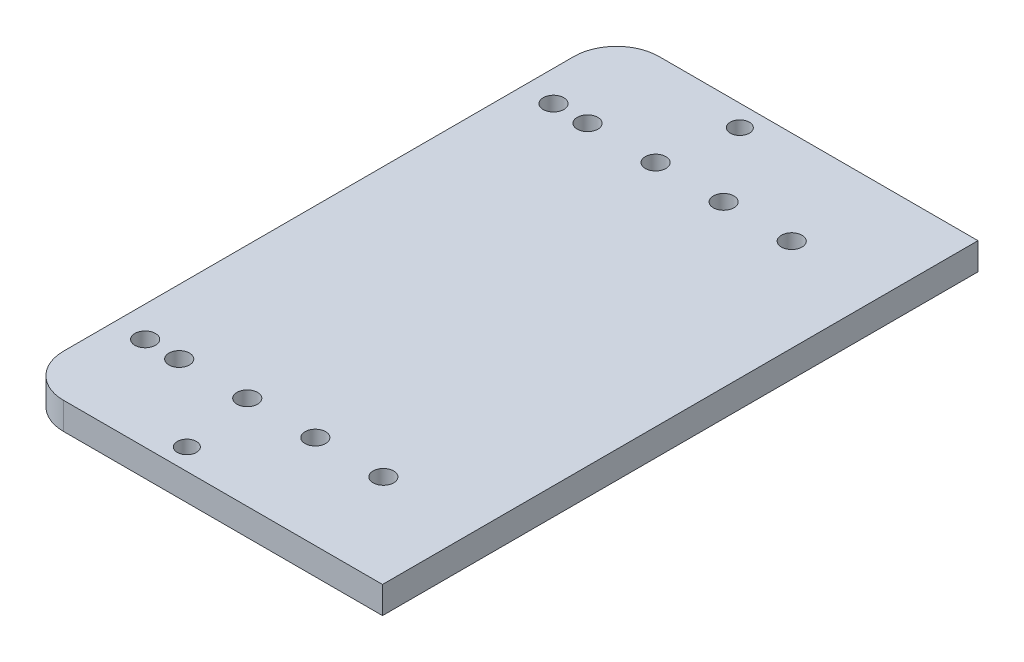
SolidWorks part; units mm, degrees
material "Acrylic (Medium-high impact)"
ref_plane "Front Plane" through (0, 0, 0) normal (0, 0, 1) x (1, 0, 0)
ref_plane "Top Plane" through (0, 0, 0) normal (0, 1, 0) x (1, 0, 0)
ref_plane "Right Plane" through (0, 0, 0) normal (1, 0, 0) x (0, 0, -1)
sketch "Sketch1" plane through (0, 0, 0) normal (0, 1, 0) x (1, 0, 0)
  line L1 (-202.6063, -35.5695) -> (-117.6063, -35.5695)
  line L2 (-202.6063, -35.5695) -> (-202.6063, -175.5695)
  line L3 (-202.6063, -175.5695) -> (-117.6063, -175.5695)
  line L4 (-117.6063, -35.5695) -> (-117.6063, -175.5695)
  dimension "D1" = 140
  dimension "D2" = 85
  dimension "D3" = 35.5695
extrude "Boss-Extrude1" add sketch "Sketch1" along normal blind 6.35
fillet "Fillet1" radius 10 2 edges at (-202.6063, 3.175, 175.5695) (-202.6063, 3.175, 35.5695)
sketch "Sketch2" plane through (0, 0, 0) normal (0, -1, 0) x (1, 0, 0)
  circle A0 centre (-139.4063, 57.5695) radius 2.425 construction
  circle A1 centre (-155.4063, 57.5695) radius 2.425 construction
  circle A2 centre (-171.4063, 57.5695) radius 2.425 construction
  circle A3 centre (-187.4063, 57.5695) radius 2.425 construction
  circle A4 centre (-195.4063, 57.5695) radius 2.425 construction
  circle A5 centre (-139.4063, 153.5695) radius 2.425 construction
  circle A6 centre (-155.4063, 153.5695) radius 2.425 construction
  circle A7 centre (-171.4063, 153.5695) radius 2.425 construction
  circle A8 centre (-187.4063, 153.5695) radius 2.425 construction
  circle A9 centre (-195.4063, 153.5695) radius 2.425 construction
  circle A10 centre (-139.4063, 57.5695) radius 2.425
  circle A11 centre (-155.4063, 57.5695) radius 2.425
  circle A12 centre (-171.4063, 57.5695) radius 2.425
  circle A13 centre (-187.4063, 57.5695) radius 2.425
  circle A14 centre (-195.4063, 57.5695) radius 2.425
  circle A15 centre (-139.4063, 153.5695) radius 2.425
  circle A16 centre (-155.4063, 153.5695) radius 2.425
  circle A17 centre (-171.4063, 153.5695) radius 2.425
  circle A18 centre (-187.4063, 153.5695) radius 2.425
  circle A19 centre (-195.4063, 153.5695) radius 2.425
extrude "Cut-Extrude1" cut sketch "Sketch2" against normal up to surface (6.35 mm away) up to face at (-171.63, 6.35, 105.5695)
sketch "Sketch3" plane through (0, 0, 0) normal (0, -1, 0) x (1, 0, 0)
  circle A0 centre (-168.6063, 170.5695) radius 2.25 construction
  circle A1 centre (-168.6063, 40.5695) radius 2.25 construction
  circle A2 centre (-168.6063, 170.5695) radius 2.25
  circle A3 centre (-168.6063, 40.5695) radius 2.25
extrude "Cut-Extrude2" cut sketch "Sketch3" against normal blind 10
